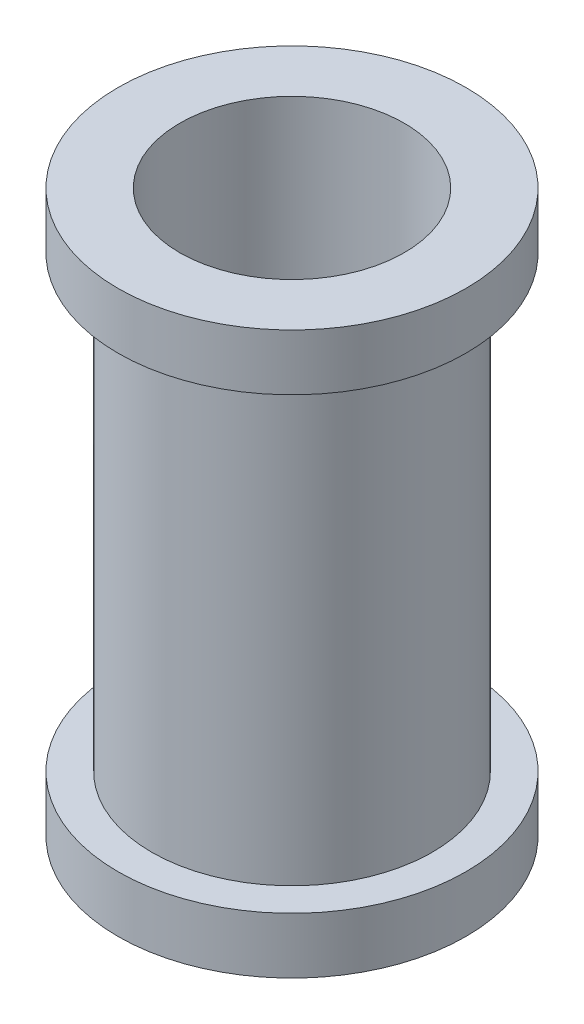
SolidWorks part; units mm, degrees
ref_plane "Front Plane" through (0, 0, 0) normal (0, 0, 1) x (1, 0, 0)
ref_plane "Top Plane" through (0, 0, 0) normal (0, 1, 0) x (1, 0, 0)
ref_plane "Right Plane" through (0, 0, 0) normal (1, 0, 0) x (0, 0, -1)
sketch "Sketch1" plane through (0, 0, 0) normal (0, 0, 1) x (1, 0, 0)
  line L0 (0, 0) -> (0, 0.5)
sketch "Sketch3" plane through (0, 0, 0) normal (0, 1, 0) x (1, 0, 0)
  circle A0 centre (0, 0) radius 0.2
sweep "Sweep-Thin1" add profiles "Sketch3" path "Sketch1" parameters "D1"=0.05
sketch "Sketch5" plane through (0, 0, 0) normal (0, 0, 1) x (1, 0, 0)
  line L0 (0, 0) -> (0, 0.1)
sketch "Sketch6" plane through (0, 0, 0) normal (0, 1, 0) x (1, 0, 0)
  circle A0 centre (0, 0) radius 0.21
sweep "Sweep-Thin2" add profiles "Sketch6" path "Sketch5" parameters "D1"=0.1
mirror "Mirror2" about plane through (0, 0.5, 0) normal (0, 1, 0) of bodies 102
